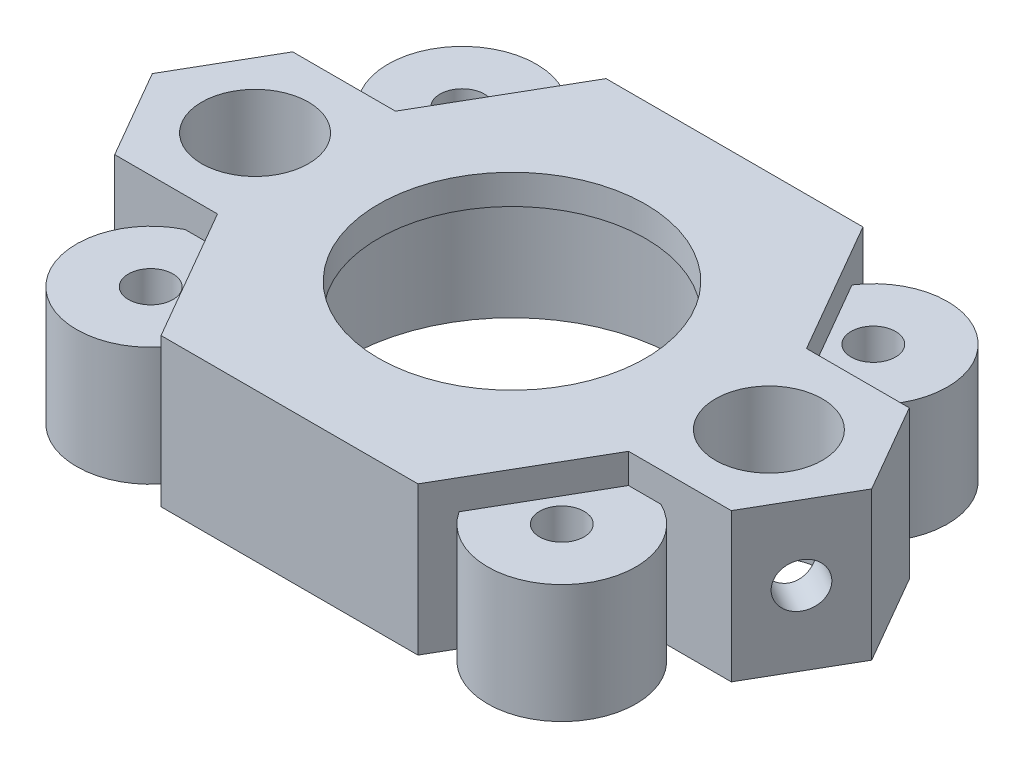
SolidWorks part; units mm, degrees
ref_plane "Front Plane" through (0, 0, 0) normal (0, 0, 1) x (1, 0, 0)
ref_plane "Top Plane" through (0, 0, 0) normal (0, 1, 0) x (1, 0, 0)
ref_plane "Right Plane" through (0, 0, 0) normal (1, 0, 0) x (0, 0, -1)
sketch "Sketch1" plane through (0, 0, 0) normal (0, 1, 0) x (1, 0, 0)
  line L0 (0, 0) -> (17.3205, 0) construction
  line L1 (17.3205, 0) -> (15.5205, 3.1177) construction
  line L2 (8.6603, 15) -> (-8.6603, 15)
  line L3 (-8.6603, 15) -> (-9.6753, 13.2419)
  line L4 (-9.6753, -13.2419) -> (-8.6603, -15)
  line L5 (-8.6603, -15) -> (8.6603, -15)
  line L6 (8.6603, -15) -> (9.6753, -13.2419)
  line L7 (0, 15) -> (0, -15) construction
  line L8 (24.2487, 0) -> (20.7846, 6)
  line L9 (20.7846, 6) -> (16.0359, 6)
  line L10 (12.1244, 3) -> (11.064, 1.1634)
  line L11 (11.064, -1.1634) -> (12.1244, -3) construction
  line L12 (16.0359, -6) -> (20.7846, -6)
  line L13 (20.7846, -6) -> (24.2487, 0)
  line L14 (-20.7846, -6) -> (-24.2487, 0)
  line L15 (-16.0359, -6) -> (-20.7846, -6)
  line L16 (-11.064, -1.1634) -> (-13.8564, -6) construction
  line L17 (-13.8564, 6) -> (-11.064, 1.1634) construction
  line L18 (-20.7846, 6) -> (-16.0359, 6)
  line L19 (-24.2487, 0) -> (-20.7846, 6)
  line L20 (-13.8564, 6) -> (-15.5205, 3.1177) construction
  line L21 (-15.5205, 3.1177) -> (-17.3205, 0) construction
  line L22 (-17.3205, 0) -> (-15.5205, -3.1177) construction
  line L23 (-11.064, 1.1634) -> (-10.3923, 0) construction
  line L24 (-10.3923, 0) -> (-11.064, -1.1634) construction
  line L25 (-15.5205, -3.1177) -> (-13.8564, -6) construction
  line L26 (11.064, 1.1634) -> (10.3923, 0) construction
  line L27 (10.3923, 0) -> (11.064, -1.1634) construction
  line L28 (12.1244, -3) -> (13.8564, -6) construction
  line L29 (15.5205, 3.1177) -> (14.3205, 5.1962) construction
  line L30 (9.6753, 13.2419) -> (8.6603, 15)
  line L31 (14.3205, -5.1962) -> (15.5205, -3.1177) construction
  line L32 (15.5205, -3.1177) -> (17.3205, 0) construction
  line L33 (13.8564, -6) -> (14.3205, -5.1962) construction
  line L34 (13.8564, 6) -> (12.1244, 3) construction
  line L35 (14.3205, 5.1962) -> (13.8564, 6) construction
  line L36 (-13.8564, 6) -> (-13.8564, 15) construction
  line L37 (-13.8564, 15) -> (-8.6603, 15) construction
  line L38 (-9.6753, 13.2419) -> (-13.8564, 6) construction
  line L39 (-16.0359, 6) -> (-13.8564, 6) construction
  line L40 (-55, 0) -> (55, 0) construction
  line L41 (-13.8564, -6) -> (-9.6753, -13.2419) construction
  line L42 (-13.8564, -6) -> (-16.0359, -6) construction
  line L43 (9.6753, -13.2419) -> (13.8564, -6) construction
  line L44 (13.8564, -6) -> (16.0359, -6) construction
  line L45 (16.0359, 6) -> (13.8564, 6) construction
  line L46 (13.8564, 6) -> (9.6753, 13.2419) construction
  line L47 (-17.3205, 0) -> (-8.6603, 15)
  circle A0 centre (0, 0) radius 11.125
  circle A1 centre (0, 0) radius 15 construction
  circle A2 centre (17.3205, 0) radius 3.6
  circle A3 centre (17.3205, 0) radius 6 construction
  circle A4 centre (-17.3205, 0) radius 3.6
  arc A5 (-9.6753, 13.2419) -> (-16.0359, 6) centre (-13.8564, 10.5) ccw
  circle A6 centre (-13.8564, 10.5) radius 1.5
  arc A7 (-13.5724, 5.5081) -> (-9.0703, 11.9469) centre (-13.8564, 10.5) ccw construction
  arc A8 (-9.0703, 11.9469) -> (-9.6753, 13.2419) centre (-13.8564, 10.5) ccw construction
  arc A9 (-13.9549, 5.501) -> (-13.5724, 5.5081) centre (-13.8564, 10.5) ccw construction
  arc A10 (-14.1404, 5.5081) -> (-13.9549, 5.501) centre (-13.8564, 10.5) ccw construction
  arc A11 (-16.0359, 6) -> (-14.1404, 5.5081) centre (-13.8564, 10.5) ccw construction
  circle A12 centre (13.8564, 10.5) radius 1.5
  arc A13 (9.6753, 13.2419) -> (16.0359, 6) centre (13.8564, 10.5) cw
  circle A14 centre (13.8564, -10.5) radius 1.5
  arc A15 (9.6753, -13.2419) -> (16.0359, -6) centre (13.8564, -10.5) ccw
  circle A16 centre (-13.8564, -10.5) radius 1.5
  arc A17 (-9.6753, -13.2419) -> (-16.0359, -6) centre (-13.8564, -10.5) cw
  dimension "D1" = 22.25
  dimension "D3" = 7.2
  dimension "D6" = 10
  dimension "D7" = 3
  dimension "D2" = 30
  dimension "D4" = 12
  dimension "D5" = 90
extrude "Boss-Extrude1" add sketch "Sketch1" along normal blind 8 contours A6 | A12 | A14 | A16 | L30 L2 L3 A5 L18 L19 L14 L15 A17 L4 L5 L6 A15 L12 L13 L8 L9 A13 | A0 | A4 | A2
sketch "Sketch2" plane through (0, 8, 0) normal (0, 1, 0) x (1, 0, 0)
  line L1 (8.6603, -15) -> (13.8564, -6)
  line L2 (17.3205, 0) -> (15.5205, 3.1177) construction
  line L3 (8.6603, 15) -> (-8.6603, 15)
  line L4 (-8.6603, 15) -> (-13.8564, 6)
  line L5 (-13.8564, -6) -> (-8.6603, -15)
  line L6 (-8.6603, -15) -> (8.6603, -15)
  line L8 (20.7846, -6) -> (24.2487, 0)
  line L9 (24.2487, 0) -> (20.7846, 6)
  line L10 (20.7846, 6) -> (13.8564, 6)
  line L11 (13.8564, 6) -> (13.7942, 5.8923) construction
  line L12 (10.3923, 0) -> (12.1244, -3) construction
  line L13 (13.8564, -6) -> (20.7846, -6)
  line L15 (-20.7846, -6) -> (-13.8564, -6)
  line L16 (-13.8564, -6) -> (-13.7942, -5.8923) construction
  line L17 (-10.3923, 0) -> (-12.1244, 3) construction
  line L18 (-13.8564, 6) -> (-20.7846, 6)
  line L19 (-20.7846, 6) -> (-24.2487, 0)
  line L20 (-24.2487, 0) -> (-20.7846, -6)
  line L21 (16.0359, -6) -> (20.7846, -6) construction
  line L22 (-16.0359, -6) -> (-20.7846, -6) construction
  line L23 (-14.3205, 5.1962) -> (-15.5205, 3.1177) construction
  line L24 (-15.5205, 3.1177) -> (-17.3205, 0) construction
  line L25 (-17.3205, 0) -> (-15.5205, -3.1177) construction
  line L26 (-15.5205, -3.1177) -> (-14.3205, -5.1962) construction
  line L27 (-14.3205, -5.1962) -> (-13.8564, -6) construction
  line L28 (-13.8564, 6) -> (-14.3205, 5.1962) construction
  line L29 (-12.1244, 3) -> (-13.7942, 5.8923) construction
  line L30 (-13.7942, 5.8923) -> (-13.8564, 6) construction
  line L31 (-12.1244, -3) -> (-10.3923, 0) construction
  line L32 (-13.7942, -5.8923) -> (-12.1244, -3) construction
  line L33 (15.5205, 3.1177) -> (14.3205, 5.1962) construction
  line L34 (13.8564, 6) -> (8.6603, 15)
  line L35 (15.5205, -3.1177) -> (17.3205, 0) construction
  line L36 (14.3205, -5.1962) -> (15.5205, -3.1177) construction
  line L37 (13.8564, -6) -> (14.3205, -5.1962) construction
  line L38 (12.1244, -3) -> (13.7942, -5.8923) construction
  line L39 (13.7942, -5.8923) -> (13.8564, -6) construction
  line L40 (12.1244, 3) -> (10.3923, 0) construction
  line L41 (13.7942, 5.8923) -> (12.1244, 3) construction
  line L42 (14.3205, 5.1962) -> (13.8564, 6) construction
  circle A0 centre (0, 0) radius 9
  circle A1 centre (-17.3205, 0) radius 3.6
  circle A2 centre (17.3205, 0) radius 3.6
  arc A3 (-13.7942, -5.8923) -> (14.1162, 5.0727) centre (0, 0) ccw construction
  circle A4 centre (17.3205, 0) radius 6 construction
  circle A5 centre (-17.3205, 0) radius 3.6 construction
  circle A6 centre (17.3205, 0) radius 3.6 construction
  arc A7 (-14.1162, 5.0727) -> (-14.1162, -5.0727) centre (-17.3205, 0) ccw construction
  arc A8 (-14.1162, -5.0727) -> (-13.7942, -5.8923) centre (0, 0) ccw construction
  arc A9 (-13.7942, 5.8923) -> (-14.1162, 5.0727) centre (0, 0) ccw construction
  arc A10 (-14.1162, 5.0727) -> (-14.1162, -5.0727) centre (0, 0) ccw construction
  arc A11 (-12.1244, 3) -> (-14.1162, 5.0727) centre (-17.3205, 0) ccw construction
  arc A12 (-14.1162, -5.0727) -> (-12.1244, -3) centre (-17.3205, 0) ccw construction
  arc A13 (-12.1244, -3) -> (-12.1244, 3) centre (-17.3205, 0) ccw construction
  arc A14 (14.1162, 5.0727) -> (13.7942, 5.8923) centre (0, 0) ccw construction
  arc A15 (13.7942, 5.8923) -> (-13.7942, 5.8923) centre (0, 0) ccw construction
  dimension "D1" = 18
extrude "Boss-Extrude2" add sketch "Sketch2" along normal blind 2
sketch "Sketch4" plane through (-18.1865, 0, 10.5) normal (-0.866, 0, 0.5) x (0.5, 0, 0.866)
  line L0 (-8.6603, 10) -> (-8.6603, 0) construction
  line L2 (-12.1244, 10) -> (-12.1244, 0) construction
  line L3 (-12.1244, 5) -> (-5.1962, 5) construction
  line L5 (-5.1962, 10) -> (-5.1962, 0) construction
  line L7 (-12.1244, 10) -> (-5.1962, 10) construction
  circle A0 centre (-8.6603, 5) radius 1.5
  dimension "D1" = 3
extrude "Cut-Extrude1" cut sketch "Sketch4" against normal up to surface and the other way through all up to face at (-17.3205, 0, -3.6)
sketch "Sketch5" plane through (18.1865, 0, 10.5) normal (0.866, 0, 0.5) x (0.5, 0, -0.866)
  line L0 (8.6603, 10) -> (8.6603, 0) construction
  line L2 (5.1962, 10) -> (5.1962, 0) construction
  line L3 (5.1962, 5) -> (12.1244, 5) construction
  line L6 (5.1962, 0) -> (12.1244, 0) construction
  circle A0 centre (8.6603, 5) radius 1.5
  dimension "D1" = 3
extrude "Cut-Extrude2" cut sketch "Sketch5" against normal up to surface (2.7274 mm away)
